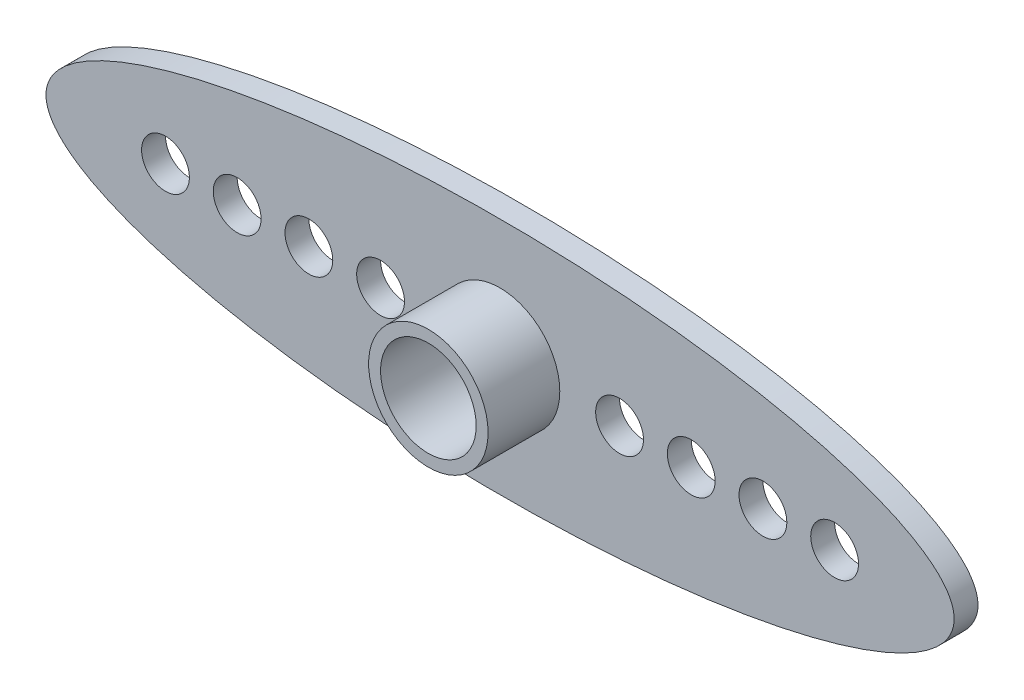
SolidWorks part; units mm, degrees
ref_plane "정면" through (0, 0, 0) normal (0, 0, 1) x (1, 0, 0)
ref_plane "윗면" through (0, 0, 0) normal (0, 1, 0) x (1, 0, 0)
ref_plane "우측면" through (0, 0, 0) normal (1, 0, 0) x (0, 0, -1)
sketch "스케치1" plane through (0, 0, 0) normal (0, 0, 1) x (1, 0, 0)
  ellipse E0 centre (0, 0) end of major axis (-19, 0) minor radius 5
  dimension "D1" = 38
  dimension "D2" = 10
extrude "보스-돌출1" add sketch "스케치1" along normal blind 1
ref_plane "평면1" through (0, 0, 1) normal (0, 0, 1) x (1, 0, 0)
sketch "스케치2" plane through (0, 0, 1) normal (0, 0, 1) x (1, 0, 0)
  line L0 (-19, 0) -> (19, 0) construction
  line L2 (0, 5) -> (0, -5) construction
  circle A0 centre (0, 0) radius 2.5
  ellipse E0 centre (0, 0) end of major axis (-19, 0) minor radius 5 construction
  dimension "D1" = 5
extrude "보스-돌출2" add sketch "스케치2" along normal blind 3
ref_plane "평면2" through (0, 0, 0) normal (0, 0, -1) x (-1, 0, 0)
sketch "스케치3" plane through (0, 0, 0) normal (0, 0, -1) x (-1, 0, 0)
  line L0 (-19, 0) -> (19, 0) construction
  line L1 (0, 5) -> (0, -5) construction
  circle A0 centre (-5, 0) radius 1
  circle A1 centre (-8, 0) radius 1
  circle A2 centre (-11, 0) radius 1
  circle A3 centre (-14, 0) radius 1
  circle A4 centre (14, 0) radius 1
  circle A5 centre (11, 0) radius 1
  circle A6 centre (8, 0) radius 1
  circle A7 centre (5, 0) radius 1
  ellipse E0 centre (0, 0) end of major axis (19, 0) minor radius 5 construction
  dimension "D5" = 2
  dimension "D6" = 2
  dimension "D7" = 2
  dimension "D8" = 2
  dimension "D1" = 5
  dimension "D2" = 3
  dimension "D3" = 3
  dimension "D4" = 3
extrude "컷-돌출1" cut sketch "스케치3" against normal through all
ref_plane "평면3" through (0, 0, 4) normal (0, 0, 1) x (1, 0, 0)
sketch "스케치4" plane through (0, 0, 4) normal (0, 0, 1) x (1, 0, 0)
  circle A0 centre (0, 0) radius 2
extrude "컷-돌출2" cut sketch "스케치4" against normal blind 3
ref_plane "평면4" through (0, 0, 0) normal (0, 0, -1) x (-1, 0, 0)
sketch "스케치5" plane through (0, 0, 0) normal (0, 0, -1) x (-1, 0, 0)
  circle A0 centre (0, 0) radius 1.5
extrude "컷-돌출3" cut sketch "스케치5" against normal blind 3
ref_plane "평면5" through (0, 0, 0) normal (0, 0, -1) x (-1, 0, 0)
sketch "스케치6" plane through (0, 0, 0) normal (0, 0, -1) x (-1, 0, 0)
  circle A0 centre (0, 0) radius 2.5
  circle A1 centre (0, 0) radius 2
  dimension "D1" = 5
  dimension "D2" = 4
extrude "보스-돌출3" add sketch "스케치6" along normal blind 1
